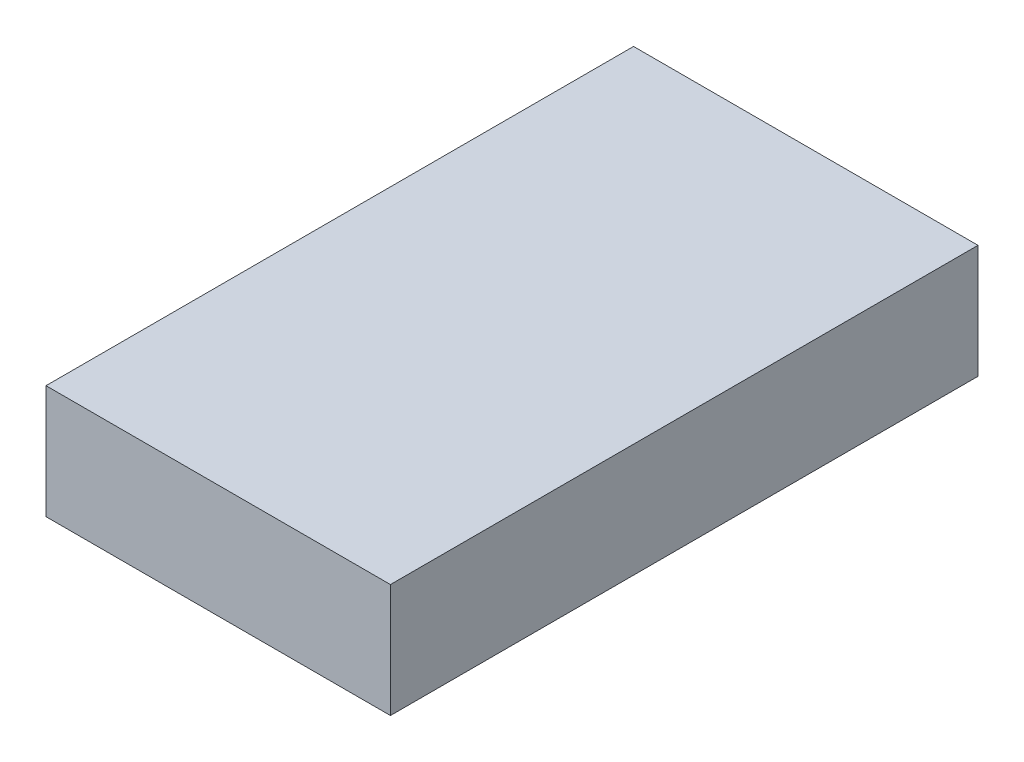
SolidWorks part; units mm, degrees
ref_plane "Front Plane" through (0, 0, 0) normal (0, 0, 1) x (1, 0, 0)
ref_plane "Top Plane" through (0, 0, 0) normal (0, 1, 0) x (1, 0, 0)
ref_plane "Right Plane" through (0, 0, 0) normal (1, 0, 0) x (0, 0, -1)
sketch "Sketch1" plane through (0, 0, 0) normal (0, 1, 0) x (1, 0, 0)
  line L1 (-42.5, -72.5) -> (42.5, -72.5)
  line L2 (-42.5, -72.5) -> (-42.5, 72.5)
  line L3 (-42.5, 72.5) -> (42.5, 72.5)
  line L4 (42.5, -72.5) -> (42.5, 72.5)
  line L5 (-42.5, -72.5) -> (42.5, 72.5) construction
  line L6 (-42.5, 72.5) -> (42.5, -72.5) construction
  point P0 (0, 0)
  dimension "D1" = 85
  dimension "D2" = 145
extrude "Boss-Extrude1" add sketch "Sketch1" along normal blind 28
